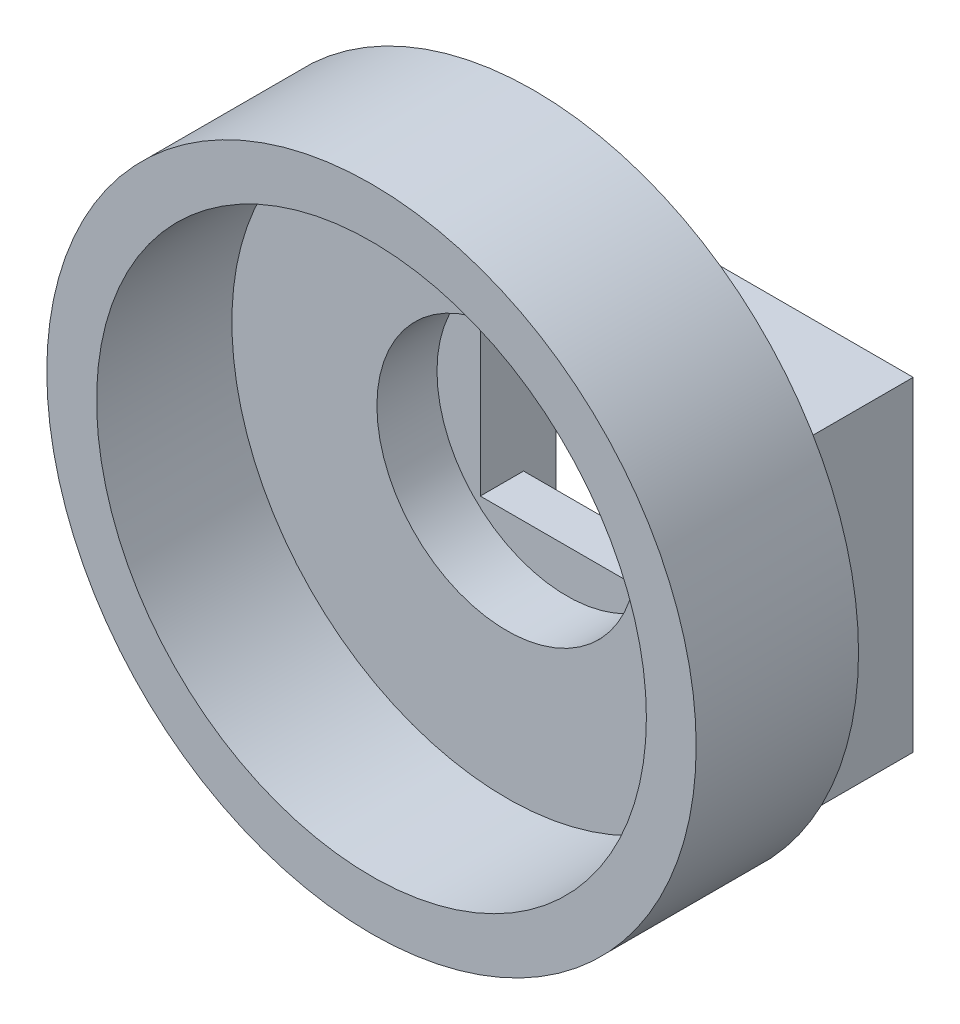
SolidWorks part; units mm, degrees
material "1060 Alloy"
ref_plane "Front Plane" through (0, 0, 0) normal (0, 0, 1) x (1, 0, 0)
ref_plane "Top Plane" through (0, 0, 0) normal (0, 1, 0) x (1, 0, 0)
ref_plane "Right Plane" through (0, 0, 0) normal (1, 0, 0) x (0, 0, -1)
sketch "Sketch1" plane through (0, 0, 0) normal (0, 0, 1) x (1, 0, 0)
  line L1 (0, 0) -> (25, 0)
  line L2 (0, 0) -> (0, 15)
  line L3 (0, 15) -> (25, 15)
  line L4 (25, 0) -> (25, 15)
  dimension "D1" = 25
  dimension "D2" = 15
extrude "Boss-Extrude1" add sketch "Sketch1" along normal blind 5.026
hole_wizard "M2 Tapped Hole1" positions "Sketch3" profile "Sketch4" tap size "M2" standard "ISO"
sketch "Sketch3" plane through (0, 0, 0) normal (0, 0, -1) x (-1, 0, 0)
  line L0 (-25, 0) -> (-25, 15) construction
  line L2 (-25, 15) -> (0, 15) construction
  line L3 (0, 15) -> (0, 0) construction
  point P0 (-23, 7.5)
  point P2 (-2, 7.5)
  dimension "D1" = 21
  dimension "D2" = 2
  dimension "D3" = 7.5
  dimension "D4" = 7.5
  dimension "D5" = 2
sketch "Sketch4" plane through (23, 7.5, 0) normal (1, 0, 0) x (0, 1, 0)
  line L0 (0, 0) -> (0, 3.9807)
  line L1 (0, 3.9807) -> (0.8, 3.5)
  line L2 (0.8, 3.5) -> (0.8, 0)
  line L5 (0.8, 0) -> (0, 0)
  line L10 (0, 3.9807) -> (-0.8, 3.5) construction
  line L11 (0, -6.35) -> (0, 107.95) construction
  dimension "Tap Drill Dia." = 1.6
  dimension "Tap Drill Depth" = 3.5
  dimension "Drill Angle" = 118
cosmetic thread "Hole Thread1" parameters "D1"=3.1, "D2"=2
cosmetic thread "Hole Thread2" parameters "D1"=3.1, "D2"=2
sketch "Sketch5" plane through (0, 0, 5.026) normal (0, 0, 1) x (1, 0, 0)
  circle A0 centre (12.5, 7.75) radius 15
  dimension "D1" = 30
  dimension "D2" = 7.75
extrude "Boss-Extrude2" add sketch "Sketch5" along normal blind 7.5
sketch "Sketch6" plane through (0, 0, 12.526) normal (0, 0, 1) x (1, 0, 0)
  circle A0 centre (12.5, 7.75) radius 12.25
  dimension "D1" = 24.5
extrude "Cut-Extrude1" cut sketch "Sketch6" against normal blind 5.25
hole_wizard "1-1/8-12 Tapped Hole2" positions "Sketch8" profile "Sketch7" tap size "1-1/8-12" standard "ANSI Inch"
sketch "Sketch8" plane through (0, 0, 12.526) normal (0, 0, 1) x (1, 0, 0)
  point P0 (12.5, 7.75)
sketch "Sketch7" plane through (12.5, 7.75, 12.526) normal (1, 0, 0) x (0, -1, 0)
  line L0 (0, 0) -> (0, 6.25)
  line L1 (0, 6.25) -> (12.7, 6.25)
  line L2 (12.7, 6.25) -> (12.7, 0)
  line L5 (12.7, 0) -> (0, 0)
  line L10 (0, 6.25) -> (-12.7, 6.25) construction
  line L11 (0, -6.35) -> (0, 107.95) construction
  dimension "Tap Drill Dia." = 25.4
  dimension "Tap Drill Depth" = 6.25
  dimension "Drill Angle" = 180
cosmetic thread "Hole Thread3" parameters "D1"=6.25, "D2"=28.575
cosmetic thread "Cosmetic Thread1" parameters "D2"=76.2
sketch "Sketch13" plane through (0, 0, 0) normal (0, 0, -1) x (-1, 0, 0)
  line L0 (-12.5, 15) -> (-12.5, 0)
  line L1 (-25, 15) -> (0, 15) construction
  line L2 (0, 0) -> (-25, 0) construction
  line L3 (-12.5, 7.5) -> (-12.5, 7.75)
  line L5 (-8.5, 3.75) -> (-16.5, 3.75)
  line L6 (-8.5, 3.75) -> (-8.5, 11.75)
  line L7 (-8.5, 11.75) -> (-16.5, 11.75)
  line L8 (-16.5, 3.75) -> (-16.5, 11.75)
  dimension "D1" = 0.25
  dimension "D2" = 8
  dimension "D3" = 8
extrude "Cut-Extrude2" cut sketch "Sketch13" against normal blind 3.5 contours L8 L5 L0 L7 | L6 L7 L0 L5
sketch "Sketch14" plane through (0, 3.75, 0) normal (0, 1, 0) x (1, 0, 0)
  line L0 (8.5, -3.5) -> (8.5, 0) construction
  line L1 (16.5, 0) -> (8.5, 0)
  line L2 (16.5, 0) -> (16.5, -1.5)
  line L3 (16.5, -1.5) -> (8.5, -1.5)
  line L4 (8.5, 0) -> (8.5, -1.5)
  dimension "D1" = 1.5
extrude "Cut-Extrude3" cut sketch "Sketch14" against normal blind 13.5
sketch "Sketch15" plane through (0, 0, 3.5) normal (0, 0, -1) x (-1, 0, 0)
  circle A0 centre (-12.5, 7.75) radius 6
  dimension "D1" = 12
extrude "Cut-Extrude4" cut sketch "Sketch15" against normal blind 13.5
